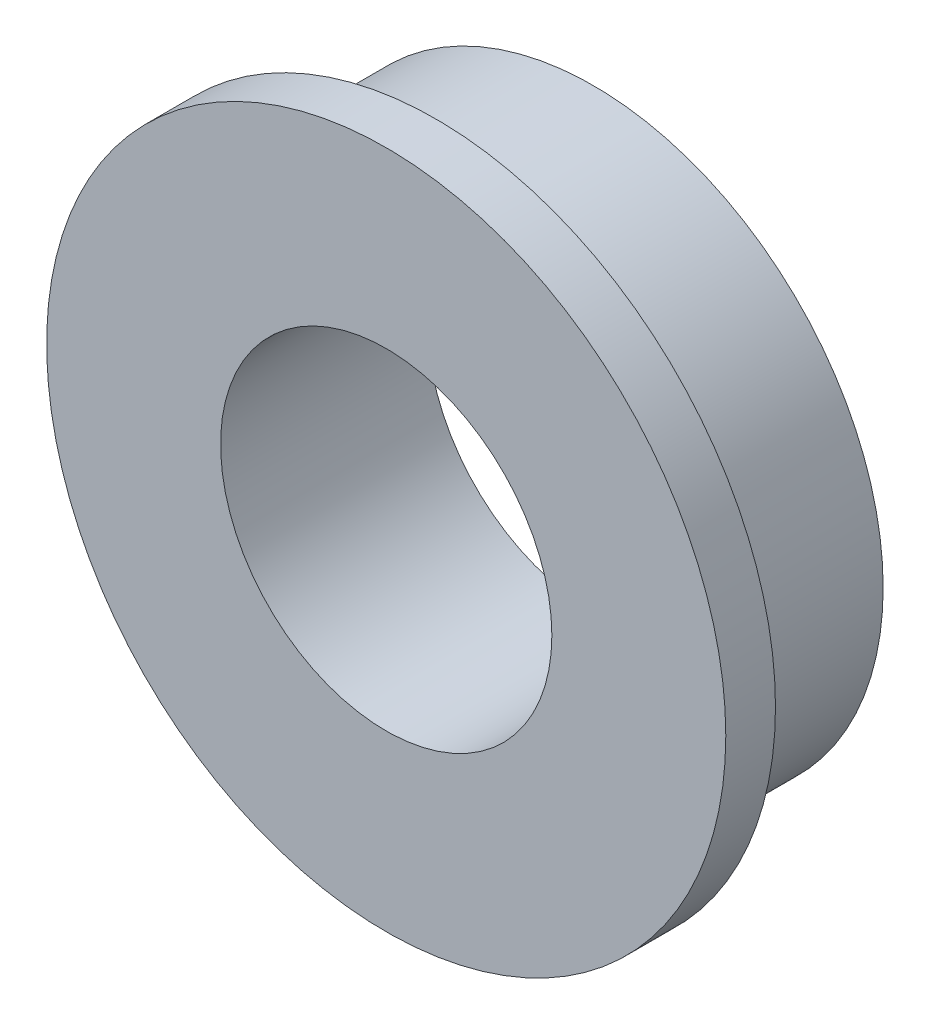
SolidWorks part; units mm, degrees
ref_plane "前视基准面" through (0, 0, 0) normal (0, 0, 1) x (1, 0, 0)
ref_plane "上视基准面" through (0, 0, 0) normal (0, 1, 0) x (1, 0, 0)
ref_plane "右视基准面" through (0, 0, 0) normal (1, 0, 0) x (0, 0, -1)
sketch "草图1" plane through (0, 0, 0) normal (0, 0, 1) x (1, 0, 0)
  circle A0 centre (0, 0) radius 3.5
  circle A1 centre (0, 0) radius 2
  dimension "D1" = 7
  dimension "D2" = 4
extrude "凸台-拉伸1" add sketch "草图1" along normal blind 1.9
sketch "草图2" plane through (0, 0, 1.9) normal (0, 0, 1) x (1, 0, 0)
  circle A0 centre (0, 0) radius 4.1
  circle A1 centre (0, 0) radius 2
  dimension "D1" = 8.2
  dimension "D2" = 4
extrude "凸台-拉伸3" add sketch "草图2" along normal blind 0.6
